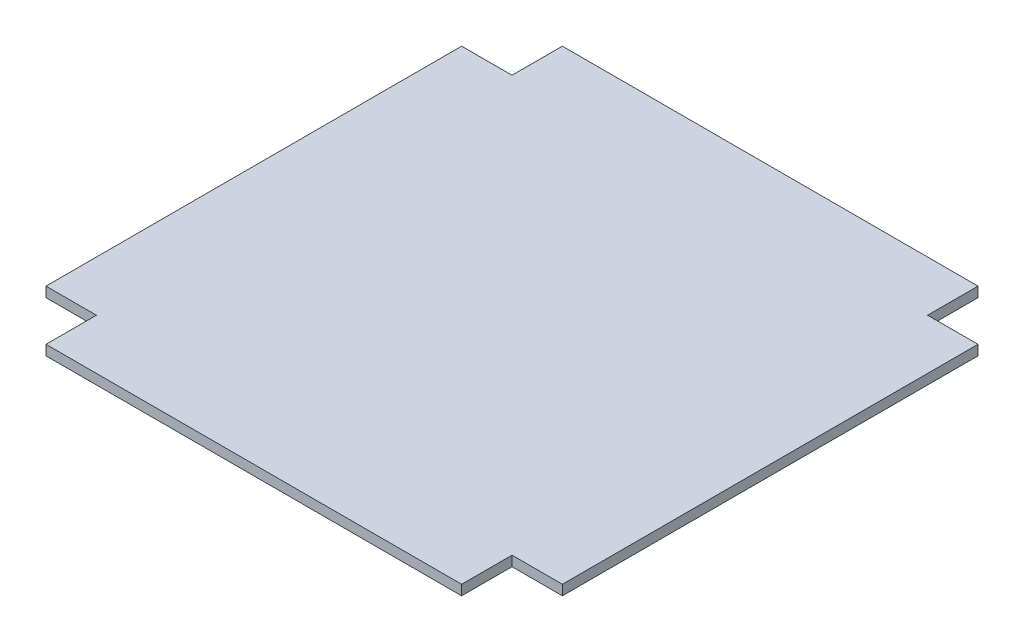
SolidWorks part; units mm, degrees
ref_plane "Front Plane" through (0, 0, 0) normal (0, 0, 1) x (1, 0, 0)
ref_plane "Top Plane" through (0, 0, 0) normal (0, 1, 0) x (1, 0, 0)
ref_plane "Right Plane" through (0, 0, 0) normal (1, 0, 0) x (0, 0, -1)
sketch "Sketch1" plane through (0, 0, 0) normal (0, 1, 0) x (1, 0, 0)
  line L0 (-103, 0) -> (103, 0) construction
  line L1 (-103, -103) -> (103, -103)
  line L2 (-103, -103) -> (-103, 103)
  line L3 (-103, 103) -> (103, 103)
  line L4 (103, -103) -> (103, 103)
  line L5 (-103, -103) -> (103, 103) construction
  line L6 (-103, 103) -> (103, -103) construction
  line L7 (-103, -103) -> (-82.9, -103)
  line L8 (-103, -103) -> (-103, -82.9)
  line L9 (-103, -82.9) -> (-82.9, -82.9)
  line L10 (-82.9, -103) -> (-82.9, -82.9)
  line L11 (0, -103) -> (0, 103) construction
  line L12 (82.9, -103) -> (82.9, -82.9)
  line L13 (103, -82.9) -> (82.9, -82.9)
  line L14 (82.9, 103) -> (82.9, 82.9)
  line L15 (103, 82.9) -> (82.9, 82.9)
  line L16 (-82.9, 103) -> (-82.9, 82.9)
  line L17 (-103, 82.9) -> (-82.9, 82.9)
  line L19 (-21, -21) -> (21, -21)
  line L20 (-21, -21) -> (-21, 21)
  line L21 (-21, 21) -> (21, 21)
  line L22 (21, -21) -> (21, 21)
  line L23 (-21, -21) -> (21, 21) construction
  line L24 (-21, 21) -> (21, -21) construction
  point P0 (0, 0)
  point P22 (0, 0)
  dimension "D1" = 206
  dimension "D2" = 20.1
  dimension "D3" = 42
extrude "Boss-Extrude1" add sketch "Sketch1" along normal blind 4 contours L17 L2 L9 L10 L1 L12 L13 L4 L15 L14 L3 L16 L22 L19 L20 L21 | L19 L22 L21 L20
